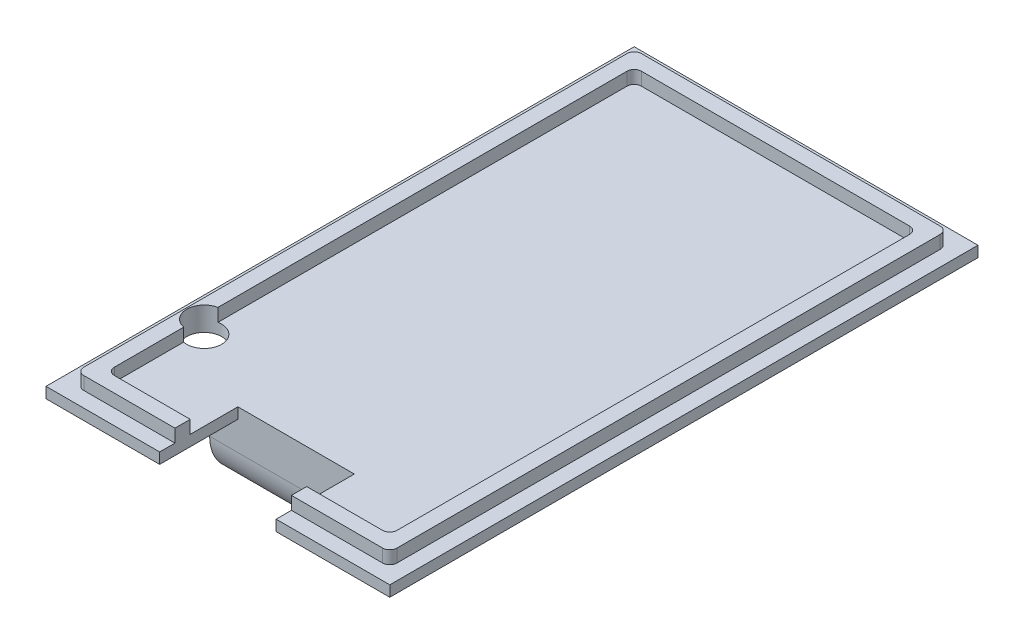
SolidWorks part; units mm, degrees
ref_plane "Front Plane" through (0, 0, 0) normal (0, 0, 1) x (1, 0, 0)
ref_plane "Top Plane" through (0, 0, 0) normal (0, 1, 0) x (1, 0, 0)
ref_plane "Right Plane" through (0, 0, 0) normal (1, 0, 0) x (0, 0, -1)
sketch "PCB Dimensions" plane through (0, 0, 0) normal (0, 1, 0) x (1, 0, 0)
  line L0 (0, 0) -> (-3.5355, 3.5355)
  line L1 (0, 0) -> (40.6457, 0)
  line L2 (0, 0) -> (0, -74.5657)
  line L3 (0, -74.5657) -> (40.6457, -74.5657)
  line L4 (40.6457, 0) -> (40.6457, -74.5657)
  line L5 (40.6457, -74.5657) -> (44.1812, -78.1012)
  line L6 (40.6457, 0) -> (44.1812, 3.5355)
  line L11 (0, -74.5657) -> (-3.5355, -78.1012)
  line L12 (44.1812, -78.1012) -> (-3.5355, -78.1012)
  line L13 (44.1812, -78.1012) -> (44.1812, 3.5355)
  line L14 (44.1812, 3.5355) -> (-3.5355, 3.5355)
  line L15 (-3.5355, -78.1012) -> (-3.5355, 3.5355)
extrude "Boss-Extrude3" add sketch "PCB Dimensions" along normal blind 1.5 contours L14 L15 L12 L13
sketch "Sketch5" plane through (0, 1.5, 0) normal (0, 1, 0) x (1, 0, 0)
  line L11 (-1.4142, 1.4142) -> (42.0599, 1.4142)
  line L12 (-1.4142, 1.4142) -> (-1.4142, -75.9799)
  line L13 (-1.4142, -75.9799) -> (42.0599, -75.9799)
  line L14 (42.0599, 1.4142) -> (42.0599, -75.9799)
  line L17 (0.7071, -0.7071) -> (39.9386, -0.7071)
  line L18 (0.7071, -0.7071) -> (0.7071, -73.8586)
  line L19 (0.7071, -73.8586) -> (39.9386, -73.8586)
  line L20 (39.9386, -0.7071) -> (39.9386, -73.8586)
extrude "Boss-Extrude4" add sketch "Sketch5" along normal blind 1.8 contours L13 L14 L11 L12 | L18 L19 L20 L17
fillet "Fillet1" radius 1 8 edges at (0.7071, 2.4, 73.8586) (-1.4142, 2.4, 75.9799) (39.9386, 2.4, 73.8586) (42.0599, 2.4, 75.9799) (0.7071, 2.4, 0.7071) (39.9386, 2.4, 0.7071) (42.0599, 2.4, -1.4142) (-1.4142, 2.4, -1.4142)
sketch "Sketch6" plane through (0, 0, 0) normal (0, -1, 0) x (1, 0, 0)
  line L0 (8.3228, 67.2497) -> (32.3228, 67.2497)
  line L1 (8.3228, 67.2497) -> (8.3228, 3.2497)
  line L2 (8.3228, 3.2497) -> (32.3228, 3.2497)
  line L3 (32.3228, 67.2497) -> (32.3228, 3.2497)
  line L4 (20.3228, 78.1012) -> (20.3228, -3.5355)
  line L5 (44.1812, 78.1012) -> (-3.5355, 78.1012) construction
  line L6 (44.1812, -3.5355) -> (-3.5355, -3.5355) construction
  line L7 (-3.5355, 37.2828) -> (44.1812, 37.2828)
  line L8 (-3.5355, 78.1012) -> (-3.5355, -3.5355) construction
  line L9 (44.1812, 78.1012) -> (44.1812, -3.5355) construction
extrude "Boss-Extrude5" add sketch "Sketch6" along normal blind 10 contours L1 L7 L4 L0 | L4 L7 L3 L0 | L7 L1 L2 L4 | L7 L4 L2 L3
sketch "Sketch7" plane through (32.3228, 0, 0) normal (1, 0, 0) x (0, 0, -1)
  line L0 (-59.2497, 0) -> (-11.2497, 0)
  line L1 (-59.2497, 0) -> (-59.2497, -6)
  line L2 (-59.2497, -6) -> (-11.2497, -6)
  line L3 (-11.2497, 0) -> (-11.2497, -6)
extrude "Cut-Extrude1" cut sketch "Sketch7" against normal blind 24
fillet "Fillet2" radius 6 2 edges at (20.3228, -10, 3.2497) (20.3228, -10, 67.2497)
fillet "Fillet3" radius 1 2 edges at (20.3228, -6, 11.2497) (20.3228, -6, 59.2497)
scale "Scale1" bodies to scale 112 scale about centroid uniform scaling yes scale factor 0.99
sketch "Sketch8" plane through (0, -0.0313, 0) normal (0, -1, 0) x (1, 0, 0)
  line L1 (43.9426, 77.6819) -> (-3.297, 77.6819) construction
  line L2 (20.3228, 77.6819) -> (12.3228, 77.6819)
  line L3 (20.3228, 77.6819) -> (28.3228, 77.6819)
  line L4 (28.3228, 77.6819) -> (28.3228, 66.939)
  line L5 (8.4428, 66.939) -> (32.2028, 66.939) construction
  line L6 (12.3228, 77.6819) -> (12.3228, 66.939)
  line L7 (12.3228, 66.939) -> (28.3228, 66.939)
extrude "Cut-Extrude2" cut sketch "Sketch8" against normal blind 10
sketch "Sketch9" plane through (0, -0.0313, 0) normal (0, -1, 0) x (1, 0, 0)
  circle A0 centre (1.373, 60.6128) radius 2.4
extrude "Cut-Extrude3" cut sketch "Sketch9" against normal blind 10
